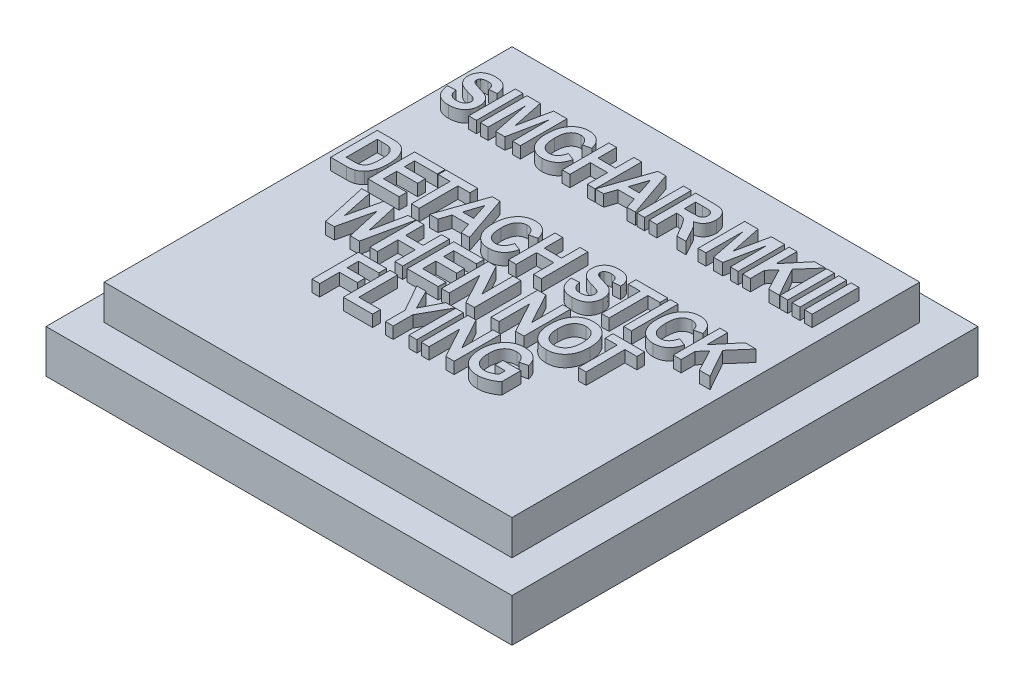
SolidWorks part; units mm, degrees
ref_plane "Спереди" through (0, 0, 0) normal (0, 0, 1) x (1, 0, 0)
ref_plane "Сверху" through (0, 0, 0) normal (0, 1, 0) x (1, 0, 0)
ref_plane "Справа" through (0, 0, 0) normal (1, 0, 0) x (0, 0, -1)
sketch "Sketch1" plane through (0, 0, 0) normal (0, 1, 0) x (1, 0, 0)
  line L1 (14.8, -14.8) -> (-14.8, -14.8)
  line L2 (14.8, -14.8) -> (14.8, 14.8)
  line L3 (14.8, 14.8) -> (-14.8, 14.8)
  line L4 (-14.8, -14.8) -> (-14.8, 14.8)
  line L5 (14.8, -14.8) -> (-14.8, 14.8) construction
  line L6 (14.8, 14.8) -> (-14.8, -14.8) construction
  point P0 (0, 0)
  dimension "D1" = 29.6
  dimension "D2" = 29.6
extrude "Boss-Extrude1" add sketch "Sketch1" along normal blind 4
sketch "Sketch2" plane through (0, 4, 0) normal (0, 1, 0) x (1, 0, 0)
  line L1 (17.5, -17.5) -> (-17.5, -17.5)
  line L2 (17.5, -17.5) -> (17.5, 17.5)
  line L3 (17.5, 17.5) -> (-17.5, 17.5)
  line L4 (-17.5, -17.5) -> (-17.5, 17.5)
  line L5 (17.5, -17.5) -> (-17.5, 17.5) construction
  line L6 (17.5, 17.5) -> (-17.5, -17.5) construction
  point P0 (0, 0)
  dimension "D1" = 35
extrude "Boss-Extrude2" add sketch "Sketch2" along normal blind 3
sketch "Sketch3" plane through (0, 7, 0) normal (0, 1, 0) x (1, 0, 0)
  line L0 (-17.5, 9.5) -> (17.5, 9.5) construction
  line L1 (-17.5, 17.5) -> (-17.5, -17.5) construction
  line L2 (17.5, -17.5) -> (17.5, 17.5) construction
  line L3 (17.5, 17.5) -> (-17.5, 17.5) construction
  text T0 "<b>SIMCHAIR MKIII</b>" font "Arial" height 4
  dimension "D1" = 8
extrude "Boss-Extrude3" add sketch "Sketch3" along normal blind 1
sketch "Sketch7" plane through (0, 7, 0) normal (0, 1, 0) x (1, 0, 0)
  line L0 (-17.5, 0.5) -> (17.5, 0.5) construction
  line L1 (-17.5, 17.5) -> (-17.5, -17.5) construction
  line L2 (17.5, -17.5) -> (17.5, 17.5) construction
  line L3 (17.5, 17.5) -> (-17.5, 17.5) construction
  text T0 "<b>DETACH STICK</b>" font "Arial" height 4
  dimension "D1" = 17
extrude "Boss-Extrude4" add sketch "Sketch7" along normal blind 1
sketch "Sketch8" plane through (0, 7, 0) normal (0, 1, 0) x (1, 0, 0)
  line L0 (-17.5, -4.5) -> (17.5, -4.5) construction
  line L1 (-17.5, 17.5) -> (-17.5, -17.5) construction
  line L2 (17.5, -17.5) -> (17.5, 17.5) construction
  line L3 (17.5, 17.5) -> (-17.5, 17.5) construction
  text T0 "<b>WHEN NOT</b>" font "Arial" height 4
  dimension "D1" = 22
extrude "Boss-Extrude5" add sketch "Sketch8" along normal blind 1
sketch "Sketch9" plane through (0, 7, 0) normal (0, 1, 0) x (1, 0, 0)
  line L0 (-17.5, -9.3635) -> (17.5, -9.3635) construction
  line L1 (-17.5, 17.5) -> (-17.5, -17.5) construction
  line L2 (17.5, -17.5) -> (17.5, 17.5) construction
  text T0 "<b>FLYING</b>" font "Arial" height 4
extrude "Boss-Extrude6" add sketch "Sketch9" along normal blind 1
chamfer "Chamfer1" distance 1 angle 60 4 edges at (14.8, 0, 0) (0, 0, 14.8) (-14.8, 0, 0) (0, 0, -14.8)
sketch "Sketch10" plane through (0, 0, 0) normal (0, -1, 0) x (1, 0, 0)
  line L1 (-15.2, 15.2) -> (15.2, 15.2)
  line L2 (-15.2, 15.2) -> (-15.2, -15.2)
  line L3 (-15.2, -15.2) -> (15.2, -15.2)
  line L4 (15.2, 15.2) -> (15.2, -15.2)
  line L5 (-15.2, 15.2) -> (15.2, -15.2) construction
  line L6 (-15.2, -15.2) -> (15.2, 15.2) construction
  line L8 (-20, -20) -> (20, -20)
  line L9 (-20, -20) -> (-20, 20)
  line L10 (-20, 20) -> (20, 20)
  line L11 (20, -20) -> (20, 20)
  line L12 (-20, -20) -> (20, 20) construction
  line L13 (14.8, 14.8) -> (14.8, -14.8) construction
  line L14 (-20, 20) -> (20, -20) construction
  point P0 (0, 0)
  point P6 (0, 0)
  point P7 (0, 0)
  dimension "D1" = 0.4
  dimension "D2" = 40
extrude "Boss-Extrude7" add sketch "Sketch10" against normal offset from surface (3.7 mm away) 0.3 separate body up to face at (0, 4, 0)
